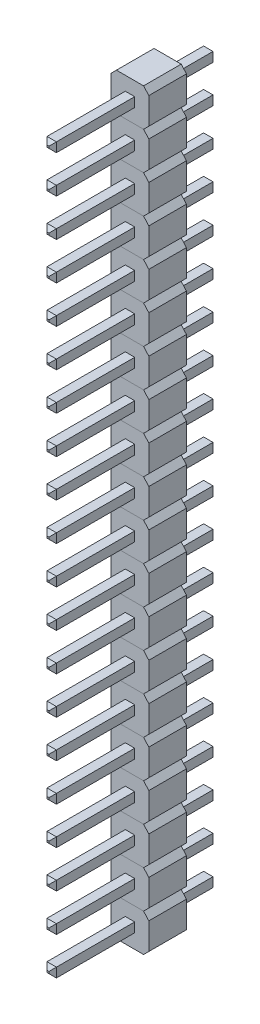
SolidWorks part; units mm, degrees
ref_plane "Alzado" through (0, 0, 0) normal (0, 0, 1) x (1, 0, 0)
ref_plane "Planta" through (0, 0, 0) normal (0, 1, 0) x (1, 0, 0)
ref_plane "Vista lateral" through (0, 0, 0) normal (1, 0, 0) x (0, 0, -1)
sketch "pin_drawing" plane through (0, 0, 0) normal (0, 0, 1) x (1, 0, 0)
  line B0 (-0.318, 0.318) -> (-1.2705, 0.318) construction
  line B1 (-0.9169, 1.25) -> (0.9169, 1.25)
  line B2 (-1.2705, 0.8964) -> (-1.2705, -0.8964)
  line B3 (-1.2705, 0.8964) -> (-0.9169, 1.25)
  line B4 (0.318, -0.318) -> (1.2705, -0.318) construction
  line B5 (-0.318, -0.318) -> (0.318, 0.318) construction
  line B6 (1.2705, 0.8564) -> (1.2705, -0.9364)
  line B7 (-0.318, 0) -> (-0.318, 0.318) construction
  line B8 (1.2705, -0.9364) -> (0.9169, -1.29)
  line B9 (0.9169, 1.25) -> (1.2705, 0.8564)
  line B10 (0.318, 0) -> (0.318, -0.318) construction
  line B11 (-0.9169, -1.29) -> (-1.2705, -0.8964)
  line B12 (-0.318, 0.318) -> (0.318, 0.318)
  line B13 (-0.318, 0.318) -> (-0.318, -0.318)
  line B14 (-0.318, -0.318) -> (0.318, -0.318)
  line B15 (0.318, 0.318) -> (0.318, -0.318)
  line B16 (0, 0) -> (0.318, -0.318) construction
  line B17 (0, 0) -> (-0.318, 0.318) construction
  line B18 (0.9169, -1.29) -> (-0.9169, -1.29)
sketch_block_instance "Block1-1"
sketch_block "Block1" parameters "D1"=0.318, "D2"=0.9525, "D3"=0.5, "D4"=135, "D5"=0.5, "D6"=135, "D7"=2.54, "D8"=2.541
extrude "Boss-Extrude1" add sketch "pin_drawing" along normal blind 2.54
sketch "Sketch1" plane through (0, 0, 2.54) normal (0, 0, 1) x (1, 0, 0)
  line L0 (-0.318, 0.318) -> (-0.318, -0.318) construction
  line L1 (0.318, -0.318) -> (0.318, 0.318) construction
  line L2 (0.318, 0.318) -> (-0.318, 0.318) construction
  line L3 (-0.318, -0.318) -> (0.318, -0.318) construction
  line L4 (0.318, -0.318) -> (0.318, 0.318)
  line L5 (0.318, 0.318) -> (-0.318, 0.318)
  line L6 (-0.318, -0.318) -> (0.318, -0.318)
  line L7 (-0.318, 0.318) -> (-0.318, -0.318)
extrude "Boss-Extrude2" add sketch "Sketch1" along normal blind 5.5372 and the other way blind 5.5372 separate body
chamfer "Chamfer1" distance 0.25 angle 45 8 edges at (0.318, 0, -2.9972) (0, 0.318, -2.9972) (-0.318, 0, -2.9972) (0, -0.318, -2.9972) (-0.318, 0, 8.0772) (0, 0.318, 8.0772) (0.318, 0, 8.0772) (0, -0.318, 8.0772)
pattern_linear "LPattern2" count 20 spacing 2.54 along (0, -1, 0) of bodies 103 105
